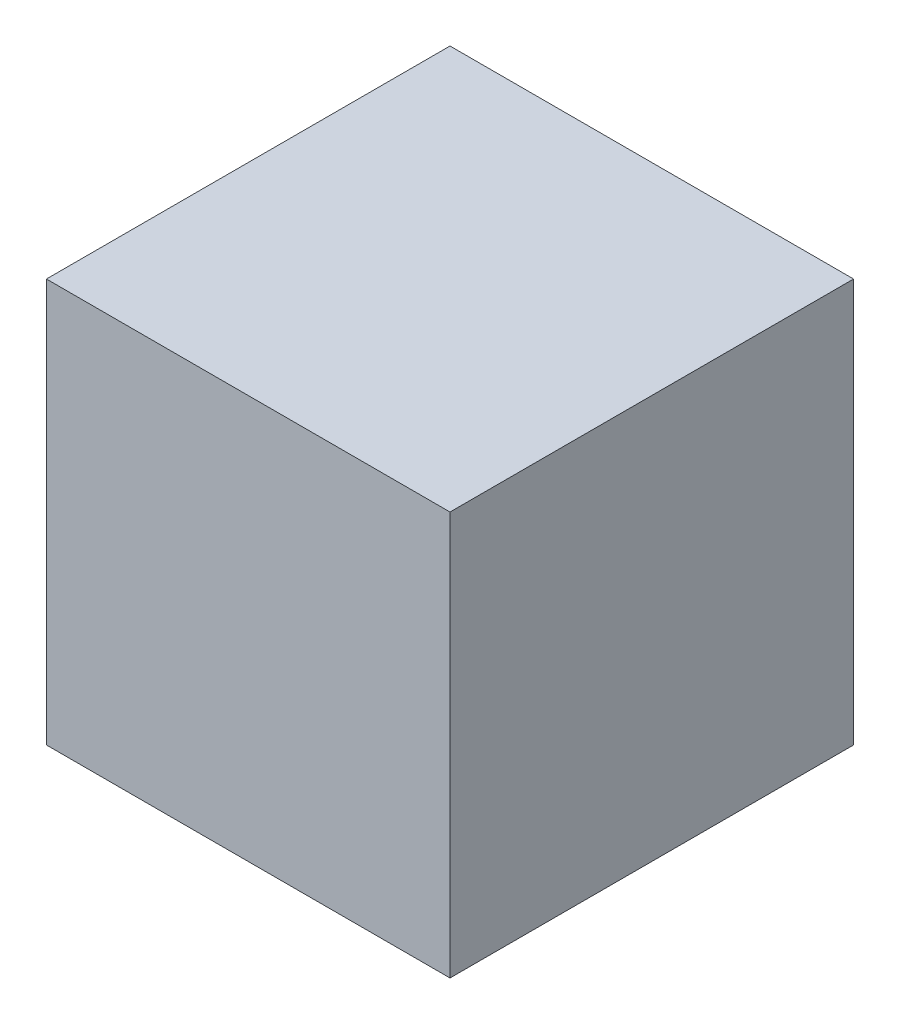
SolidWorks part; units mm, degrees
ref_plane "정면" through (0, 0, 0) normal (0, 0, 1) x (1, 0, 0)
ref_plane "윗면" through (0, 0, 0) normal (0, 1, 0) x (1, 0, 0)
ref_plane "우측면" through (0, 0, 0) normal (1, 0, 0) x (0, 0, -1)
sketch "스케치1" plane through (0, 0, 0) normal (0, 1, 0) x (1, 0, 0)
  line L1 (-15, 15) -> (15, 15)
  line L2 (-15, 15) -> (-15, -15)
  line L3 (-15, -15) -> (15, -15)
  line L4 (15, 15) -> (15, -15)
  point P4 (0, 15)
  point P6 (15, 0)
  dimension "D1" = 30
  dimension "D2" = 30
extrude "보스-돌출1" add sketch "스케치1" along normal blind 30
sketch "스케치2" plane through (0, 0, 0) normal (0, 0, 1) x (1, 0, 0)
  line L1 (-15, 30) -> (-15, 0) construction
  line L2 (-17.5, 15) -> (-4.5, 15) construction
  line L3 (-17.5, 15) -> (-4.5, 15)
  arc A0 (-4.5, 15) -> (-17.5, 15) centre (-11, 15) ccw
  point P1 (-15, 15)
  point P4 (-17.5, 15)
  point P8 (0, 0)
  dimension "D2" = 6.5
  dimension "D1" = 2.5
revolve "회전1" add sketch "스케치2" angle 360 about L2
